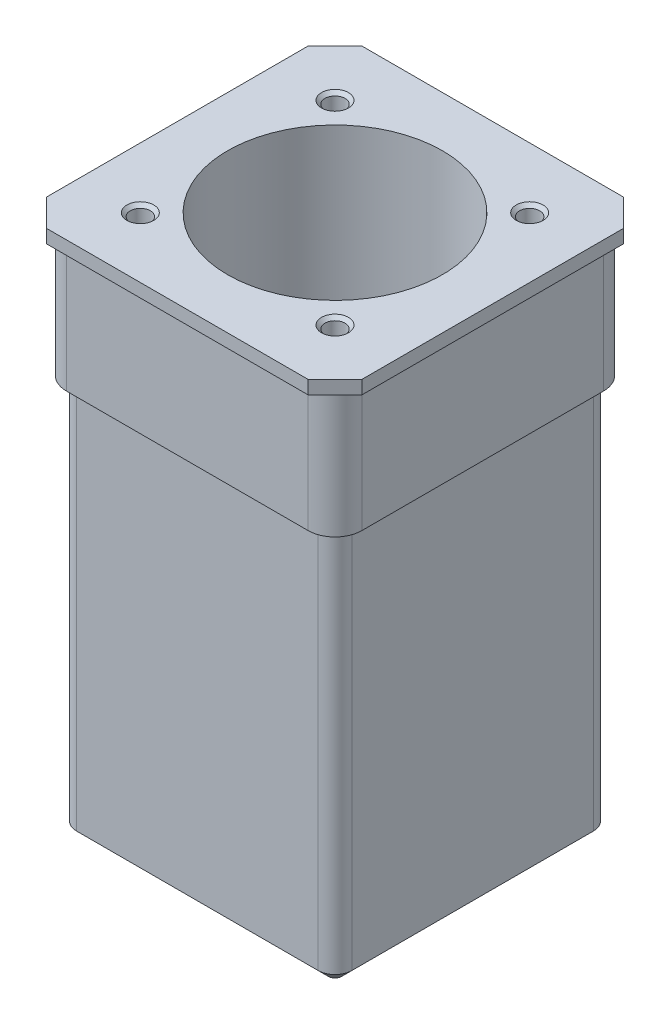
SolidWorks part; units mm, degrees
material "Ст 3 ГОСТ 380-2005"
ref_plane "Спереди" through (0, 0, 0) normal (0, 0, 1) x (1, 0, 0)
ref_plane "Сверху" through (0, 0, 0) normal (0, 1, 0) x (1, 0, 0)
ref_plane "Слева" through (0, 0, 0) normal (1, 0, 0) x (0, 0, -1)
sketch "Эскиз1" plane through (0, 0, 0) normal (0, 1, 0) x (1, 0, 0)
  line L1 (-20.5, -20.5) -> (20.5, -20.5)
  line L2 (-20.5, -20.5) -> (-20.5, 20.5)
  line L3 (-20.5, 20.5) -> (20.5, 20.5)
  line L4 (20.5, -20.5) -> (20.5, 20.5)
  line L5 (-20.5, -20.5) -> (20.5, 20.5) construction
  line L6 (-20.5, 20.5) -> (20.5, -20.5) construction
  point P0 (0, 0)
  dimension "D1" = 41
extrude "Вытянуть1" add sketch "Эскиз1" along normal blind 59
sketch "Эскиз2" plane through (0, 59, 0) normal (0, 1, 0) x (1, 0, 0)
  line L1 (-22, -22) -> (22, -22)
  line L2 (-22, -22) -> (-22, 22)
  line L3 (-22, 22) -> (22, 22)
  line L4 (22, -22) -> (22, 22)
  line L5 (-22, -22) -> (22, 22) construction
  line L6 (-22, 22) -> (22, -22) construction
  point P0 (0, 0)
  dimension "D1" = 44
extrude "Вытянуть2" add sketch "Эскиз2" along normal blind 19
sketch "Эскиз3" plane through (0, 78, 0) normal (0, 1, 0) x (1, 0, 0)
  line L0 (22, -22) -> (22, 22) construction
  line L1 (-23.5, 23.5) -> (23.5, 23.5)
  line L2 (-23.5, 23.5) -> (-23.5, -23.5)
  line L3 (-23.5, -23.5) -> (23.5, -23.5)
  line L4 (23.5, 23.5) -> (23.5, -23.5)
  line L5 (-23.5, 23.5) -> (23.5, -23.5) construction
  line L6 (-23.5, -23.5) -> (23.5, 23.5) construction
  point P0 (0, 0)
  dimension "D1" = 47
  dimension "D2" = 1.5
extrude "Вытянуть3" add sketch "Эскиз3" along normal blind 2
fillet "Скругление1" radius 2.5 4 edges at (-20.5, 29.5, -20.5) (-20.5, 29.5, 20.5) (20.5, 29.5, -20.5) (20.5, 29.5, 20.5)
fillet "Скругление2" radius 4 4 edges at (22, 68.5, -22) (-22, 68.5, -22) (-22, 68.5, 22) (22, 68.5, 22)
chamfer "Фаска1" distance 1.5 angle 45 8 edges at (0, 0, -20.5) (-19.7678, 0, -19.7678) (19.7678, 0, -19.7678) (-20.5, 0, 0) (20.5, 0, 0) (-19.7678, 0, 19.7678) (19.7678, 0, 19.7678) (0, 0, 20.5)
chamfer "Фаска2" distance 4 angle 45 4 edges at (-23.5, 79, -23.5) (-23.5, 79, 23.5) (23.5, 79, -23.5) (23.5, 79, 23.5)
sketch "Эскиз4" plane through (0, 80, 0) normal (0, 1, 0) x (1, 0, 0)
  circle A0 centre (0, 0) radius 16
  dimension "D1" = 32
extrude "Вытянуть4" cut sketch "Эскиз4" against normal through all
sketch "Эскиз5" plane through (0, 0, 0) normal (0, -1, 0) x (1, 0, 0)
  line L0 (-21.5, -21.5) -> (21.5, 21.5) construction
  line L1 (-23.5, -19.5) -> (-19.5, -23.5) construction
  line L2 (23.5, 19.5) -> (19.5, 23.5) construction
  line L3 (-21.5, 21.5) -> (21.5, -21.5) construction
  line L4 (-19.5, 23.5) -> (-23.5, 19.5) construction
  line L5 (19.5, -23.5) -> (23.5, -19.5) construction
  line L6 (18, 19) -> (-18, 19) construction
  circle A0 centre (-14.4975, 14.4975) radius 4.5025 construction
  circle A1 centre (0, 0) radius 16 construction
  circle A2 centre (0, 0) radius 20.5 construction
  dimension "D1" = 9.0051
  dimension "D2" = 41
sketch "Эскиз8" plane through (0, 80, 0) normal (0, 1, 0) x (1, 0, 0)
  line L0 (-21.5, 21.5) -> (21.5, -21.5) construction
  line L1 (-21.5, -21.5) -> (21.5, 21.5) construction
  line L2 (-21.5, 21.5) -> (21.5, -21.5)
  line L3 (-21.5, -21.5) -> (21.5, 21.5)
  circle A0 centre (0, 0) radius 20.5 construction
  circle A1 centre (0, 0) radius 20.5
hole_wizard "Отверстие обработанное метчиком M4x0.71" positions "Трехмерный эскиз1" profile "Эскиз7" tap size "M4x0.7" standard "ГОСТ"
sketch3d "Трехмерный эскиз1"
  line L0 (-21.5, 0, 21.5) -> (21.5, 0, -21.5) construction
  line L1 (-21.5, 0, -21.5) -> (21.5, 0, 21.5) construction
  line L2 (-21.5, 80, -21.5) -> (21.5, 80, 21.5) construction
  line L3 (-21.5, 80, 21.5) -> (21.5, 80, -21.5) construction
  circle A0 centre (0, 0, 0) radius 20.5 construction
  circle A1 centre (0, 80, 0) radius 20.5 construction
  point P0 (-14.4957, 0, 14.4957)
  point P2 (-14.4957, 0, -14.4957)
  point P4 (14.4957, 0, -14.4957)
  point P6 (14.4957, 0, 14.4957)
  point P12 (0, -20.5, 0)
  point P23 (-14.4957, 80, 14.4957)
  point P25 (14.4957, 80, 14.4957)
  point P27 (14.4957, 80, -14.4957)
  point P29 (-14.4957, 80, -14.4957)
  point P38 (0, 100.5, 0)
sketch "Эскиз7" plane through (-14.4957, 0, 14.4957) normal (1, 0, 0) x (0, 0, -1)
  line L0 (0, 0) -> (0, 14.9013)
  line L1 (0, 14.9013) -> (1.5, 14)
  line L2 (1.5, 14) -> (1.5, 0.5)
  line L3 (1.5, 0.5) -> (2, 0)
  line L5 (2, 0) -> (0, 0)
  line L6 (-1.5, 0.5) -> (-2, 0) construction
  line L10 (0, 14.9013) -> (-1.5, 14) construction
  line L11 (0, -6.35) -> (0, 107.95) construction
  dimension "Диаметр сверла" = 3
  dimension "Глубина сверла" = 14
  dimension "Диаметр передней зенковки" = 4
  dimension "Угол передней зенковки" = 90
  dimension "Угол заточки сверла" = 118
cosmetic thread "Отверстие резьбы1" parameters "D1"=10, "D2"=4
cosmetic thread "Отверстие резьбы2" parameters "D1"=10, "D2"=4
cosmetic thread "Отверстие резьбы3" parameters "D1"=10, "D2"=4
cosmetic thread "Отверстие резьбы4" parameters "D1"=10, "D2"=4
cosmetic thread "Отверстие резьбы5" parameters "D1"=12, "D2"=4
cosmetic thread "Отверстие резьбы6" parameters "D1"=12, "D2"=4
cosmetic thread "Отверстие резьбы7" parameters "D1"=12, "D2"=4
cosmetic thread "Отверстие резьбы8" parameters "D1"=12, "D2"=4
